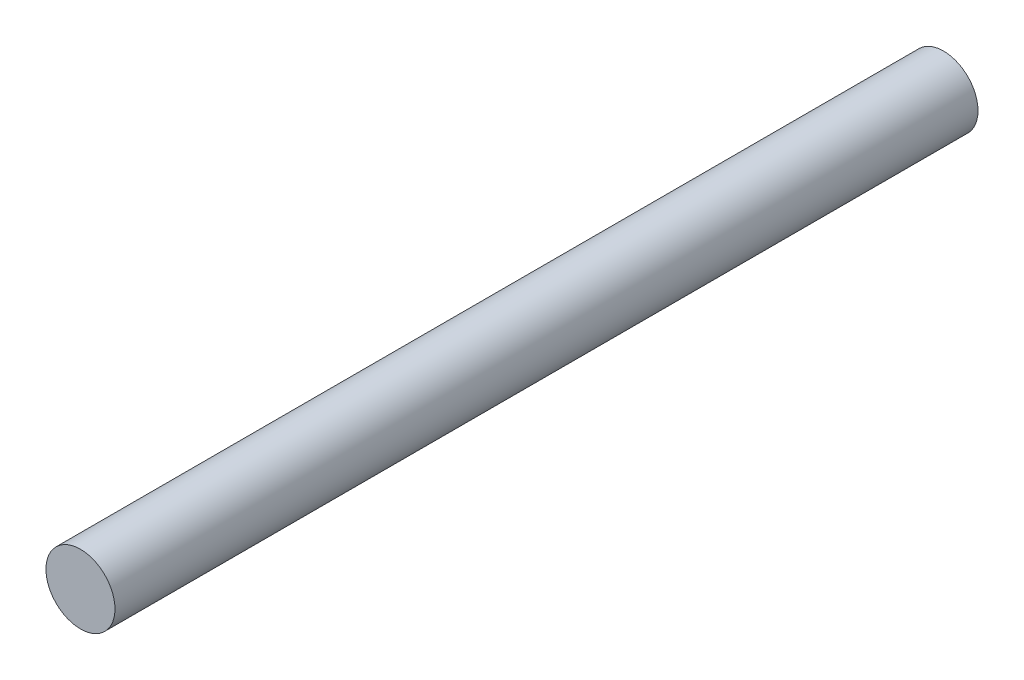
SolidWorks part; units mm, degrees
ref_plane "Front Plane" through (0, 0, 0) normal (0, 0, 1) x (1, 0, 0)
ref_plane "Top Plane" through (0, 0, 0) normal (0, 1, 0) x (1, 0, 0)
ref_plane "Right Plane" through (0, 0, 0) normal (1, 0, 0) x (0, 0, -1)
sketch "Sketch1" plane through (0, 0, 0) normal (0, 0, 1) x (1, 0, 0)
  circle A0 centre (0, 0) radius 1
  dimension "D1" = 2
extrude "Boss-Extrude1" add sketch "Sketch1" along normal blind 25
